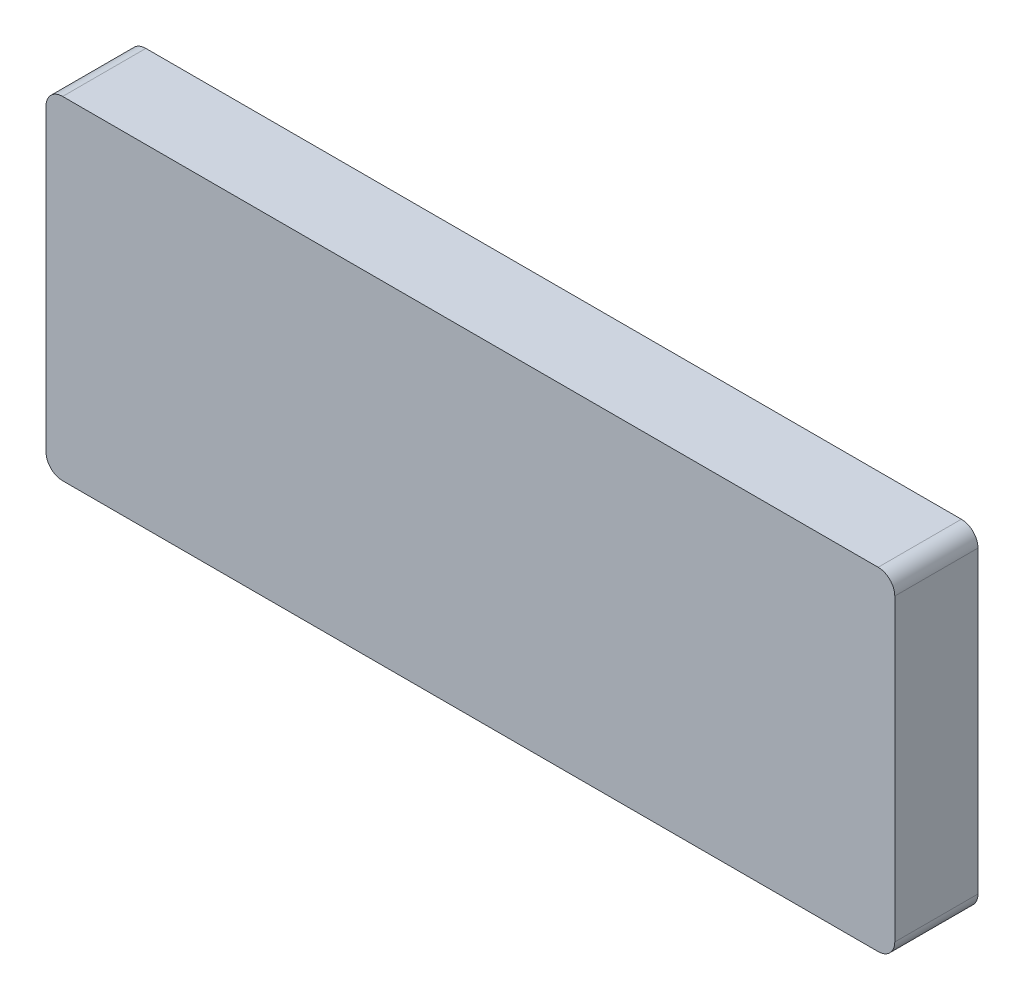
SolidWorks part; units mm, degrees
ref_plane "Front Plane" through (0, 0, 0) normal (0, 0, 1) x (1, 0, 0)
ref_plane "Top Plane" through (0, 0, 0) normal (0, 1, 0) x (1, 0, 0)
ref_plane "Right Plane" through (0, 0, 0) normal (1, 0, 0) x (0, 0, -1)
sketch "Sketch2" plane through (0, 0, 0) normal (0, 0, 1) x (1, 0, 0)
  line L0 (-5, 5.1169) -> (-5, -5.1169)
  line L1 (-4.2428, -5.5457) -> (4.2854, -0.4287)
  line L2 (4.2854, 0.4287) -> (-4.2428, 5.5457)
  line L3 (10, 4.5) -> (10, -4.5)
  line L4 (10.5, -5) -> (12.5, -5)
  line L5 (13, -4.5) -> (13, -2)
  line L6 (13, -2) -> (21.2969, -5.6875)
  line L7 (22, -5.2306) -> (22, 5.2306)
  line L8 (21.2969, 5.6875) -> (13, 2)
  line L9 (13, 2) -> (13, 4.5)
  line L10 (12.5, 5) -> (10.5, 5)
  line L12 (-21.5, 2) -> (-10.5, 2)
  line L13 (-22, 1.5) -> (-22, -1.5)
  line L14 (-21.5, -2) -> (-10.5, -2)
  line L15 (-10, 1.5) -> (-10, -1.5)
  arc A0 (21.2969, 5.6875) -> (22, 5.2306) centre (21.5, 5.2306) cw
  arc A1 (22, -5.2306) -> (21.2969, -5.6875) centre (21.5, -5.2306) cw
  arc A2 (12.5, -5) -> (13, -4.5) centre (12.5, -4.5) ccw
  arc A3 (10.5, -5) -> (10, -4.5) centre (10.5, -4.5) cw
  arc A4 (13, 4.5) -> (12.5, 5) centre (12.5, 4.5) ccw
  arc A5 (10, 4.5) -> (10.5, 5) centre (10.5, 4.5) cw
  arc A6 (4.2854, -0.4287) -> (4.2854, 0.4287) centre (4.0282, 0) ccw
  arc A7 (-4.2428, -5.5457) -> (-5, -5.1169) centre (-4.5, -5.1169) cw
  arc A8 (-4.2428, 5.5457) -> (-5, 5.1169) centre (-4.5, 5.1169) ccw
  arc A9 (-10.5, 2) -> (-10, 1.5) centre (-10.5, 1.5) cw
  arc A10 (-10.5, -2) -> (-10, -1.5) centre (-10.5, -1.5) ccw
  arc A11 (-22, -1.5) -> (-21.5, -2) centre (-21.5, -1.5) ccw
  arc A12 (-22, 1.5) -> (-21.5, 2) centre (-21.5, 1.5) cw
  dimension "D1" = 0.5
sketch "Sketch3" plane through (0, 0, 0) normal (0, 0, 1) x (1, 0, 0)
  line L1 (-24, 10) -> (25, 10)
  line L2 (-25, 9) -> (-25, -9)
  line L3 (-24, -10) -> (25, -10)
  line L4 (26, 9) -> (26, -9)
  arc A0 (25, 10) -> (26, 9) centre (25, 9) cw
  arc A1 (26, -9) -> (25, -10) centre (25, -9) cw
  arc A2 (-24, -10) -> (-25, -9) centre (-24, -9) cw
  arc A3 (-24, 10) -> (-25, 9) centre (-24, 9) ccw
  dimension "D1" = 1
ref_plane "Plane1" through (0, 0, 5) normal (0, 0, 1) x (1, 0, 0)
sketch "Sketch4" plane through (0, 0, 5) normal (0, 0, 1) x (1, 0, 0)
  line L0 (-5, 5.1169) -> (-5, -5.1169)
  line L1 (-4.2428, -5.5457) -> (4.2854, -0.4287)
  line L2 (4.2854, 0.4287) -> (-4.2428, 5.5457)
  line L3 (10, 4.5) -> (10, -4.5)
  line L4 (10.5, -5) -> (12.5, -5)
  line L5 (13, -4.5) -> (13, -2)
  line L6 (13, -2) -> (21.2969, -5.6875)
  line L7 (22, -5.2306) -> (22, 5.2306)
  line L8 (21.2969, 5.6875) -> (13, 2)
  line L9 (13, 2) -> (13, 4.5)
  line L10 (12.5, 5) -> (10.5, 5)
  line L12 (-21.5, 2) -> (-10.5, 2)
  line L13 (-22, 1.5) -> (-22, -1.5)
  line L14 (-21.5, -2) -> (-10.5, -2)
  line L15 (-10, 1.5) -> (-10, -1.5)
  arc A0 (21.2969, 5.6875) -> (22, 5.2306) centre (21.5, 5.2306) cw
  arc A1 (22, -5.2306) -> (21.2969, -5.6875) centre (21.5, -5.2306) cw
  arc A2 (12.5, -5) -> (13, -4.5) centre (12.5, -4.5) ccw
  arc A3 (10.5, -5) -> (10, -4.5) centre (10.5, -4.5) cw
  arc A4 (13, 4.5) -> (12.5, 5) centre (12.5, 4.5) ccw
  arc A5 (10, 4.5) -> (10.5, 5) centre (10.5, 4.5) cw
  arc A6 (4.2854, -0.4287) -> (4.2854, 0.4287) centre (4.0282, 0) ccw
  arc A7 (-4.2428, -5.5457) -> (-5, -5.1169) centre (-4.5, -5.1169) cw
  arc A8 (-4.2428, 5.5457) -> (-5, 5.1169) centre (-4.5, 5.1169) ccw
  arc A9 (-10.5, 2) -> (-10, 1.5) centre (-10.5, 1.5) cw
  arc A10 (-10.5, -2) -> (-10, -1.5) centre (-10.5, -1.5) ccw
  arc A11 (-22, -1.5) -> (-21.5, -2) centre (-21.5, -1.5) ccw
  arc A12 (-22, 1.5) -> (-21.5, 2) centre (-21.5, 1.5) cw
  dimension "D1" = 0.5
extrude "Boss-Extrude1" add sketch "Sketch3" along normal blind 5
sketch "Sketch5" plane through (0, 0, 5) normal (0, 0, 1) x (1, 0, 0)
  line L11 (-4.5, 5.1169) -> (-4.5, -5.1169)
  line L16 (-4.5, -5.1169) -> (4.0282, 0)
  line L17 (4.0282, 0) -> (-4.5, 5.1169)
  line L18 (10.5, 4.5) -> (10.5, -4.5)
  line L19 (10.5, -4.5) -> (12.5, -4.5)
  line L20 (12.5, -4.5) -> (12.5, -1.2306)
  line L21 (12.5, -1.2306) -> (21.5, -5.2306)
  line L22 (21.5, -5.2306) -> (21.5, 5.2306)
  line L23 (21.5, 5.2306) -> (12.5, 1.2306)
  line L24 (12.5, 1.2306) -> (12.5, 4.5)
  line L25 (12.5, 4.5) -> (10.5, 4.5)
  line L26 (-21.5, 1.5) -> (-10.5, 1.5)
  line L27 (-10.5, 1.5) -> (-10.5, -1.5)
  line L28 (-21.5, -1.5) -> (-10.5, -1.5)
  line L29 (-21.5, 1.5) -> (-21.5, -1.5)
